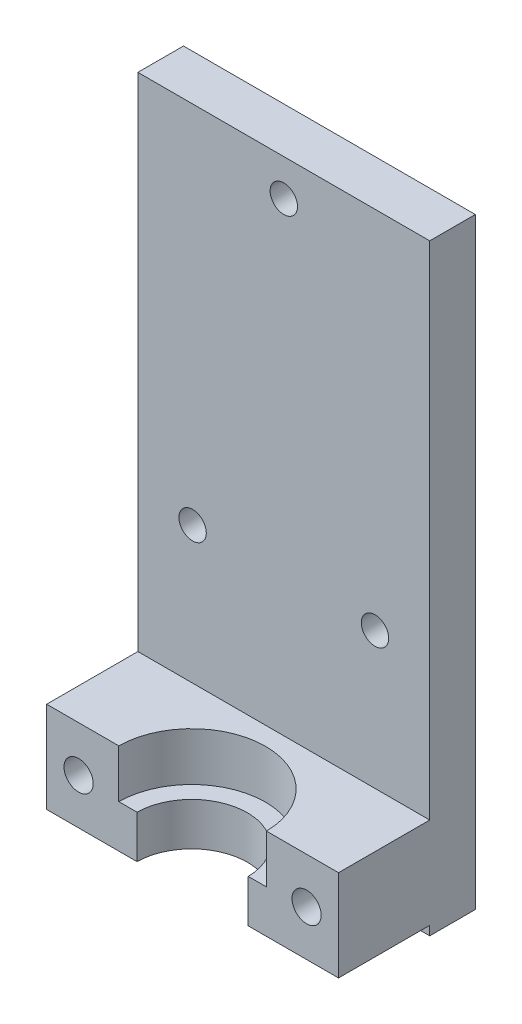
SolidWorks part; units mm, degrees
ref_plane "Front Plane" through (0, 0, 0) normal (0, 0, 1) x (1, 0, 0)
ref_plane "Top Plane" through (0, 0, 0) normal (0, 1, 0) x (1, 0, 0)
ref_plane "Right Plane" through (0, 0, 0) normal (1, 0, 0) x (0, 0, -1)
sketch "Sketch1" plane through (0, 0, 0) normal (0, 0, 1) x (1, 0, 0)
  line L1 (0, 0) -> (32, 0)
  line L2 (0, 0) -> (0, -66)
  line L3 (0, -66) -> (32, -66)
  line L4 (32, 0) -> (32, -66)
  circle A1 centre (16, -4) radius 1.5
  circle A2 centre (6, -40) radius 1.5
  circle A3 centre (26, -40) radius 1.5
  dimension "D3" = 40
  dimension "D4" = 3
  dimension "D5" = 3
  dimension "D6" = 3
  dimension "D7" = 40
  dimension "D8" = 20
  dimension "D9" = 6
  dimension "D11" = 16
  dimension "D1" = 66
  dimension "D2" = 32
  dimension "D10" = 4
  dimension "D14" = 16
extrude "Boss-Extrude1" add sketch "Sketch1" along normal blind 25
sketch "Sketch3" plane through (0, 0, 0) normal (-1, 0, 0) x (0, 0, 1)
  line L1 (25, 0) -> (5, 0)
  line L2 (25, 0) -> (25, -55)
  line L3 (25, -55) -> (5, -55)
  line L4 (5, 0) -> (5, -55)
  line L5 (25, -66) -> (5, -66)
  line L6 (25, -66) -> (25, -65)
  line L7 (25, -65) -> (5, -65)
  line L8 (5, -66) -> (5, -65)
  dimension "D1" = 55
  dimension "D2" = 20
  dimension "D3" = 10
  dimension "D4" = 20
extrude "Cut-Extrude1" cut sketch "Sketch3" against normal through all
sketch "Sketch4" plane through (0, -55, 0) normal (0, 1, 0) x (1, 0, 0)
  line L6 (32, -5) -> (0, -5) construction
  line L7 (0, -5) -> (0, -25) construction
  circle A0 centre (15.9997, -15.1) radius 6.1
  point P6 (0, -15)
  dimension "D1" = 12.2
  dimension "D2" = 4
  dimension "D3" = 16
extrude "Cut-Extrude6" cut sketch "Sketch4" against normal through all
sketch "Sketch5" plane through (0, -55, 0) normal (0, 1, 0) x (1, 0, 0)
  circle A0 centre (15.9997, -15.1) radius 8.1
  dimension "D1" = 16.2
extrude "Cut-Extrude7" cut sketch "Sketch5" against normal blind 5.3
sketch "Sketch7" plane through (0, 0, 25) normal (0, 0, 1) x (1, 0, 0)
  line L0 (32, -55) -> (0, -55) construction
  line L1 (32, -55) -> (0, -55) construction
  line L3 (32, -65) -> (32, -55) construction
  circle A0 centre (3.5, -60) radius 1.6
  circle A1 centre (28.5, -60) radius 1.6
  dimension "D1" = 3.2
  dimension "D2" = 3.2
  dimension "D5" = 25
  dimension "D3" = 5
  dimension "D4" = 5
  dimension "D6" = 3.5
extrude "Cut-Extrude8" cut sketch "Sketch7" against normal through all
sketch "Sketch9" plane through (0, 0, 0) normal (0, 0, -1) x (-1, 0, 0)
  line L1 (-27.2191, -57.232) -> (-30.2567, -57.5067)
  line L2 (-30.2567, -57.5067) -> (-31.5376, -60.2747)
  line L3 (-31.5376, -60.2747) -> (-29.7809, -62.768)
  line L4 (-29.7809, -62.768) -> (-26.7433, -62.4933)
  line L5 (-26.7433, -62.4933) -> (-25.4624, -59.7253)
  line L6 (-25.4624, -59.7253) -> (-27.2191, -57.232)
  line L7 (-4.846, -57.2631) -> (-6.5433, -59.7972)
  line L8 (-6.5433, -59.7972) -> (-5.1972, -62.5342)
  line L9 (-5.1972, -62.5342) -> (-2.154, -62.7369)
  line L10 (-2.154, -62.7369) -> (-0.4567, -60.2028)
  line L11 (-0.4567, -60.2028) -> (-1.8028, -57.4658)
  line L12 (-1.8028, -57.4658) -> (-4.846, -57.2631)
  circle A0 centre (-28.5, -60) radius 2.6414 construction
  circle A1 centre (-3.5, -60) radius 2.6414 construction
  dimension "D1" = 6.1
  dimension "D2" = 6.1
extrude "Cut-Extrude9" cut sketch "Sketch9" against normal blind 10
sketch "Sketch10" plane through (0, 0, 25) normal (0, 0, 1) x (1, 0, 0)
  line L1 (0, -55) -> (32, -55)
  line L2 (0, -55) -> (0, -65)
  line L3 (0, -65) -> (32, -65)
  line L4 (32, -55) -> (32, -65)
extrude "Cut-Extrude10" cut sketch "Sketch10" against normal blind 10
